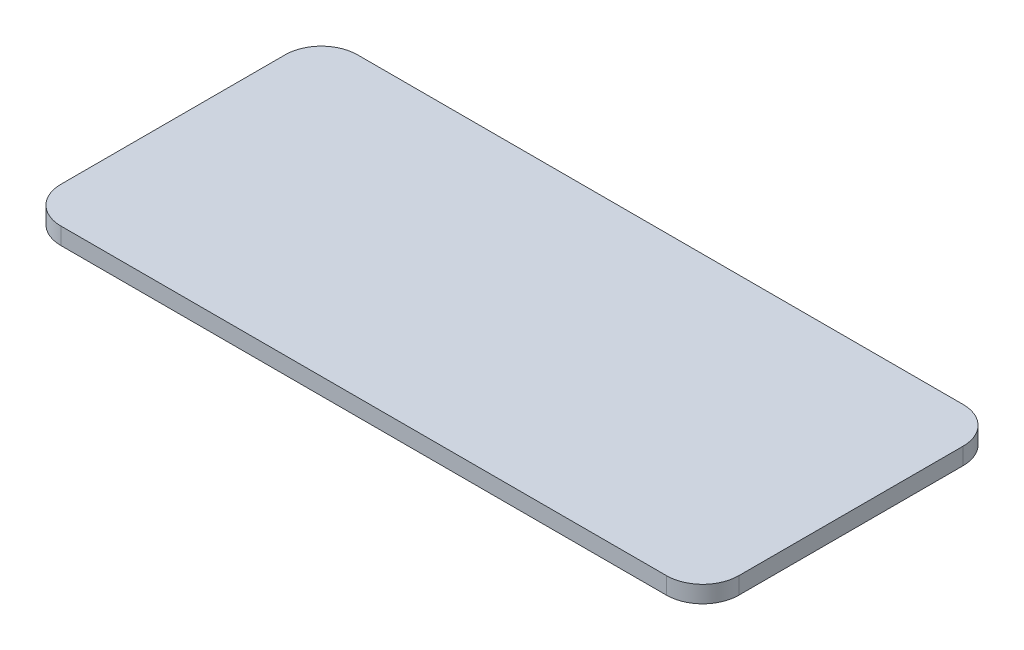
SolidWorks part; units mm, degrees
ref_plane "Front Plane" through (0, 0, 0) normal (0, 0, 1) x (1, 0, 0)
ref_plane "Top Plane" through (0, 0, 0) normal (0, 1, 0) x (1, 0, 0)
ref_plane "Right Plane" through (0, 0, 0) normal (1, 0, 0) x (0, 0, -1)
sketch "Sketch1" plane through (0, 0, 0) normal (0, 1, 0) x (1, 0, 0)
  line L1 (32, 14) -> (-32, 14)
  line L2 (32, 14) -> (32, -14)
  line L3 (32, -14) -> (-32, -14)
  line L4 (-32, 14) -> (-32, -14)
  line L5 (32, 14) -> (-32, -14) construction
  line L6 (32, -14) -> (-32, 14) construction
  point P0 (0, 0)
  dimension "D1" = 64
  dimension "D2" = 28
extrude "Boss-Extrude1" add sketch "Sketch1" along normal blind 1.6
fillet "Fillet1" radius 3.41 4 edges at (-32, 0.8, -14) (32, 0.8, -14) (-32, 0.8, 14) (32, 0.8, 14)
